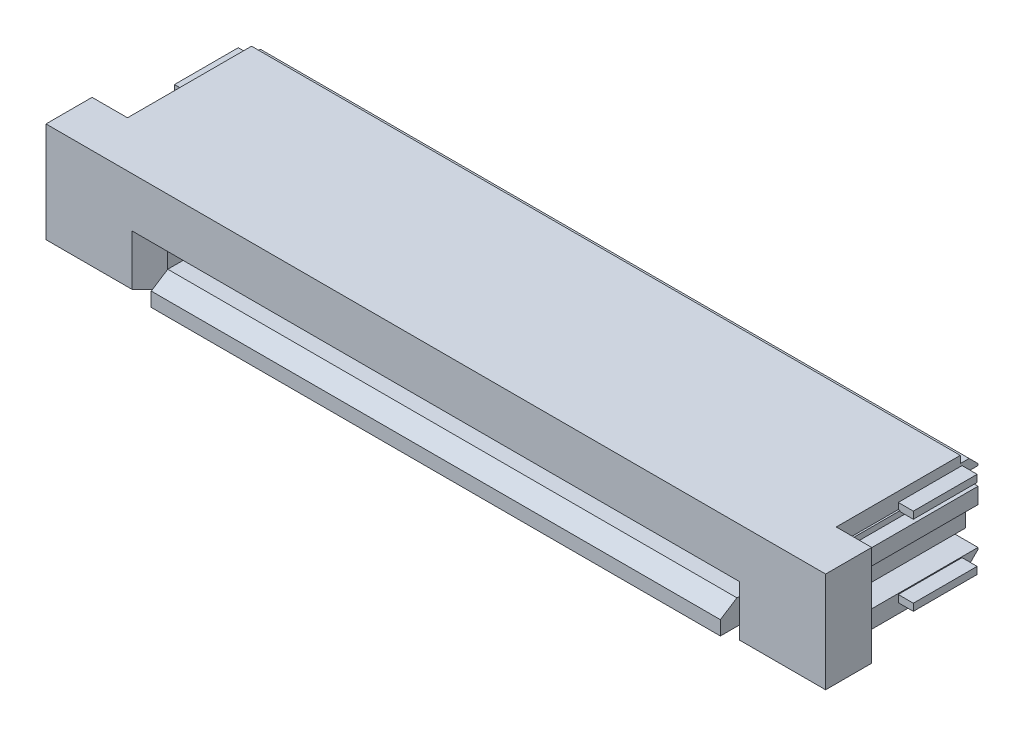
SolidWorks part; units mm, degrees
material "policarbonato"
ref_plane "Front" through (0, 0, 0) normal (0, 0, 1) x (1, 0, 0)
ref_plane "Top" through (0, 0, 0) normal (0, 1, 0) x (1, 0, 0)
ref_plane "Side" through (0, 0, 0) normal (1, 0, 0) x (0, 0, -1)
sketch "Sketch1" plane through (0, 0, 0) normal (1, 0, 0) x (0, 0, -1)
  line L0 (-1.75, 1.5) -> (1.75, 1.5)
  line L1 (2, 1.3) -> (1.75, 1.3)
  line L2 (1.75, 1.5) -> (1.75, 1.3)
  line L3 (2.25, 1.05) -> (2, 1.3)
  line L4 (2.25, -1.05) -> (2.25, 1.05)
  line L5 (2, -1.3) -> (2.25, -1.05)
  line L6 (1.75, -1.3) -> (1.75, -1.5)
  line L7 (2, -1.3) -> (1.75, -1.3)
  line L8 (-3.05, -1.5) -> (1.75, -1.5)
  line L9 (-1.75, -0.65) -> (-1.75, 1.5)
  line L10 (-2.35, -0.65) -> (-1.75, -0.65)
  line L11 (-2.35, -0.65) -> (-3.05, -1.1)
  line L12 (-3.05, -1.5) -> (-3.05, -1.1)
  line L13 (-1.75, 1.5) -> (1.75, -1.5) construction
  point P1 (0, 0)
  dimension "D1" = 45
  dimension "D2" = 45
  dimension "D3" = 3.5
  dimension "D4" = 0.25
  dimension "D5" = 0.5
  dimension "D6" = 0.2
  dimension "D7" = 1.3
  dimension "D8" = 32.735
  dimension "D9" = 0.6
  dimension "D10" = 3
  dimension "D11" = 0.4
  dimension "D12" = 0.2
extrude "Base" add sketch "Sketch1" along normal mid plane 20
sketch "Sketch2" plane through (0, 0, 3.05) normal (0, 0, 1) x (1, 0, 0)
  line L0 (10, -1.5) -> (-10, -1.5) construction
  line L1 (-8.1, 0.75) -> (8.1, 0.75)
  line L2 (-8.1, 0.75) -> (-8.1, -0.8)
  line L3 (-8.1, -0.8) -> (8.1, -0.8)
  line L4 (8.1, 0.75) -> (8.1, -0.8)
  line L5 (10, 1.5) -> (-10, 1.5) construction
  line L6 (-10, 1.5) -> (-10, -0.65) construction
  line L7 (10, 1.5) -> (10, -0.65) construction
  dimension "D1" = 0.7
  dimension "D2" = 0.75
  dimension "D3" = 1.9
  dimension "D4" = 1.9
extrude "Card Slot" cut sketch "Sketch2" against normal blind 3.8
sketch "Sketch4" plane through (0, 0, 1.75) normal (0, 0, 1) x (1, 0, 0)
  line L0 (10, 1.5) -> (10, -0.65) construction
  line L1 (-10, 1) -> (-8.225, 1)
  line L2 (-10, 1) -> (-10, -1)
  line L3 (-10, -1) -> (-8.225, -1)
  line L4 (-8.225, 1) -> (-8.225, -1)
  line L5 (10, 1) -> (8.225, 1)
  line L6 (10, 1) -> (10, -1)
  line L7 (10, -1) -> (8.225, -1)
  line L8 (8.225, 1) -> (8.225, -1)
  line L9 (10, -1.5) -> (-10, -1.5) construction
  line L11 (10, 1.5) -> (-10, 1.5) construction
  line L12 (-10, 1.5) -> (-10, -0.65) construction
  dimension "D1" = 0.5
  dimension "D2" = 0.5
  dimension "D3" = 1.775
extrude "Wings" cut sketch "Sketch4" against normal through all
sketch "Sketch5" plane through (0, 0, 3.05) normal (0, 0, 1) x (1, 0, 0)
  line L0 (10, -1.5) -> (-10, -1.5) construction
  line L1 (-10, 1.5) -> (-8.03, 1.5)
  line L2 (-10, 1.5) -> (-10, -1.5)
  line L3 (-10, -1.5) -> (-8.03, -1.5)
  line L4 (-8.03, 1.5) -> (-8.03, -1.5)
  line L5 (0, 0) -> (0, 2.0181) construction
  line L6 (10, 1.5) -> (8.03, 1.5)
  line L7 (10, 1.5) -> (10, -1.5)
  line L8 (10, -1.5) -> (8.03, -1.5)
  line L9 (8.03, 1.5) -> (8.03, -1.5)
  dimension "D1" = 1.97
extrude "Front Lead In" cut sketch "Sketch5" against normal up to surface (1.3 mm away) up to face at (0, 0.4917, 1.75)
chamfer "Card Slot Lead In" distance 0.1 angle 60 3 edges at (8.1, -0.025, 1.75) (0, 0.75, 1.75) (-8.1, -0.025, 1.75)
ref_plane "POS 1 Plane" through (7, 0, 0) normal (1, 0, 0) x (0, 0, -1)
ref_plane "WT Plane" through (0, 0, 0) normal (0, 0, 1) x (1, 0, 0)
sketch "Sketch8" plane through (0, 0, 0) normal (0, 0, 1) x (1, 0, 0)
  line L0 (0, 0) -> (0, 411) construction
  line L1 (-10, -1) -> (-10, -1.5) construction
  line L4 (10, -1.5) -> (10, -1.3) construction
  line L5 (10, 1.5) -> (-10, 1.5) construction
  point P8 (10, -1.4)
  line B0 (-10.425, 1.025) -> (-8.575, 1.025)
  line B1 (-8.575, 1.225) -> (-10.425, 1.225)
  line B2 (-10.425, 1.025) -> (-10.425, 1.225)
  line B3 (-8.225, -0.875) -> (-8.225, 0.875)
  line B4 (-8.425, 0.875) -> (-8.425, -0.875)
  line B5 (-8.575, -1.025) -> (-10.425, -1.025)
  line B6 (-10.425, -1.225) -> (-10.425, -1.025)
  line B7 (-10.425, -1.225) -> (-8.575, -1.225)
  arc B8 (-8.225, 0.875) -> (-8.575, 1.225) centre (-8.575, 0.875) ccw
  arc B9 (-8.425, 0.875) -> (-8.575, 1.025) centre (-8.575, 0.875) ccw
  arc B10 (-8.575, -1.225) -> (-8.225, -0.875) centre (-8.575, -0.875) ccw
  arc B11 (-8.575, -1.025) -> (-8.425, -0.875) centre (-8.575, -0.875) ccw
  line B12 (10.425, 1.025) -> (8.575, 1.025)
  line B13 (8.575, 1.225) -> (10.425, 1.225)
  line B14 (10.425, 1.025) -> (10.425, 1.225)
  line B15 (8.225, -0.875) -> (8.225, 0.875)
  line B16 (8.425, 0.875) -> (8.425, -0.875)
  line B17 (8.575, -1.025) -> (10.425, -1.025)
  line B18 (10.425, -1.225) -> (10.425, -1.025)
  line B19 (10.425, -1.225) -> (8.575, -1.225)
  arc B20 (8.225, 0.875) -> (8.575, 1.225) centre (8.575, 0.875) cw
  arc B21 (8.425, 0.875) -> (8.575, 1.025) centre (8.575, 0.875) cw
  arc B22 (8.575, -1.225) -> (8.225, -0.875) centre (8.575, -0.875) cw
  arc B23 (8.575, -1.025) -> (8.425, -0.875) centre (8.575, -0.875) cw
  dimension "D1" = 0.425
  dimension "D2" = 0.425
  dimension "D3" = 0.275
sketch_block_instance "Block2-1"
sketch_block "Block2"
sketch_block_instance "Block2-3"
extrude "WT" add sketch "Sketch8" against normal blind 1.8
sketch "Sketch9" plane through (0, 0, 1.75) normal (0, 0, 1) x (1, 0, 0)
  line L1 (-10, -1.5) -> (-8.03, -1.5) construction
  line L2 (8.07, 0.1) -> (8.07, -1.33)
  line L3 (-8.07, 0.1) -> (8.07, 0.1)
  line L4 (8.07, -1.33) -> (11, -1.33)
  line L5 (11, -1.33) -> (11, 1.5)
  line L6 (11, 1.5) -> (-11, 1.5)
  line L7 (-11, 1.5) -> (-11, -1.33)
  line L8 (-11, -1.33) -> (-8.07, -1.33)
  line L9 (-8.07, -1.33) -> (-8.07, 0.1)
  line L10 (-10.425, 1.225) -> (-10.425, 1.025) construction
  point P2 (0, 0.1)
  dimension "D1" = 0.1
  dimension "D2" = 2.83
  dimension "D3" = 2.93
  dimension "D4" = 0.575
  dimension "D5" = 0.17
extrude "Gate" add sketch "Sketch9" along normal blind 1.3
chamfer "Gate Chamfer" distance 0.5 angle 45 2 edges at (8.07, -0.615, 3.05) (-8.07, -0.615, 3.05)
sketch "Sketch10" plane through (0, 0, 1.75) normal (0, 0, -1) x (-1, 0, 0)
  line L0 (-11, -1.33) -> (-11, 1.5) construction
  line L1 (-10.05, -0.3) -> (-10.05, 0.4451)
  line L2 (-9.5, -0.3) -> (-10.05, -0.3)
  line L3 (-11, 1.5) -> (-10, 1.5) construction
  line L4 (9.125, -0.2019) -> (9.125, 0.3755)
  line L5 (0, 0) -> (0, 3.8889) construction
  line L6 (-9.4, 0.3755) -> (-9.125, 0.3755)
  line L7 (-9.4, 0.3755) -> (-9.4, 1.05)
  line L8 (-9.4, 1.05) -> (-10.05, 1.05)
  line L9 (-10.05, 1.05) -> (-10.05, 0.8951)
  line L10 (-10.05, 0.8951) -> (-10.4, 0.8951)
  line L11 (-10.4, 0.8951) -> (-10.4, 0.4451)
  line L12 (-10.4, 0.4451) -> (-10.05, 0.4451)
  line L13 (9.5, -0.2019) -> (9.125, -0.2019)
  line L14 (-9.5, -0.3) -> (-9.5, -0.2019)
  line L15 (-9.5, -0.2019) -> (-9.125, -0.2019)
  line L16 (9.5, -0.3) -> (9.5, -0.2019)
  line L17 (-9.125, -0.2019) -> (-9.125, 0.3755)
  line L18 (10.4, 0.4451) -> (10.05, 0.4451)
  line L19 (10.4, 0.8951) -> (10.4, 0.4451)
  line L20 (10.05, 0.8951) -> (10.4, 0.8951)
  line L21 (10.05, 1.05) -> (10.05, 0.8951)
  line L22 (9.4, 1.05) -> (10.05, 1.05)
  line L23 (9.4, 0.3755) -> (9.4, 1.05)
  line L24 (9.4, 0.3755) -> (9.125, 0.3755)
  line L25 (9.5, -0.3) -> (10.05, -0.3)
  line L26 (10.05, -0.3) -> (10.05, 0.4451)
  dimension "D1" = 1.35
  dimension "D2" = 0.65
  dimension "D3" = 0.35
  dimension "D4" = 0.45
  dimension "D5" = 0.35
  dimension "D6" = 0.7451
  dimension "D7" = 0.55
  dimension "D8" = 0.0981
  dimension "D9" = 0.375
  dimension "D10" = 0.6
  dimension "D11" = 0.45
  dimension "D12" = 0.275
  dimension "D13" = 0.6745
extrude "Gate Guide" add sketch "Sketch10" along normal blind 3.6
sketch "Sketch6" plane through (7, 0, 0) normal (1, 0, 0) x (0, 0, -1)
  line L0 (-1.75, -1.5) -> (1.75, -1.5) construction
  line L3 (0.75, 0.75) -> (0.75, -0.8) construction
  line B0 (1.8966, 1.1164) -> (1.8966, 1.1134)
  line B1 (1.1383, -0.6804) -> (-1.1565, -0.4395)
  line B2 (1.1383, -0.6804) -> (1.5518, -0.6804)
  line B3 (1.8966, -0.6772) -> (1.8966, -0.6743)
  line B4 (2.2503, -0.3242) -> (2.2503, -0.6772)
  line B5 (2.2503, 0.5618) -> (2.2503, -0.1226)
  line B6 (3.7503, 1.3984) -> (3.7503, 1.3222)
  line B7 (2.5059, 0.815) -> (2.3646, 0.815)
  line B8 (3.069, 1.176) -> (2.7405, 0.9004)
  line B9 (3.6487, 1.2206) -> (3.1915, 1.2206)
  line B10 (3.1915, 1.5) -> (3.6487, 1.5)
  line B11 (2.6097, 1.1553) -> (2.8894, 1.3901)
  line B12 (1.5518, 1.1196) -> (-1.3757, 1.1196)
  line B13 (-1.0668, 0.7796) -> (-1.4132, 0.9796)
  line B14 (1.3415, 0.5196) -> (1.3415, 0.449)
  line B15 (1.0915, 0.7696) -> (-1.0293, 0.7696)
  line B16 (-1.1045, -0.2363) -> (0.5626, -0.3004)
  line B17 (-1.6498, -0.425) -> (-1.3625, -0.0694)
  arc B18 (1.6915, -0.5407) -> (1.5518, -0.6804) centre (1.5518, -0.5407) cw
  arc B19 (1.6915, -0.5407) -> (1.8966, -0.6743) centre (1.7506, -0.6743) cw
  arc B20 (2.2503, -0.6772) -> (1.8966, -0.6772) centre (2.0735, -0.6772) cw
  arc B21 (2.2503, -0.3242) -> (2.2503, -0.1226) centre (2.3646, -0.2234) cw
  arc B22 (3.6487, 1.5) -> (3.7503, 1.3984) centre (3.6487, 1.3984) cw
  arc B23 (3.7503, 1.3222) -> (3.6487, 1.2206) centre (3.6487, 1.3222) cw
  arc B24 (2.2503, 0.5618) -> (2.3646, 0.815) centre (2.3646, 0.6626) cw
  arc B25 (2.7405, 0.9004) -> (2.5059, 0.815) centre (2.5059, 1.18) cw
  arc B26 (3.069, 1.176) -> (3.1915, 1.2206) centre (3.1915, 1.0301) cw
  arc B27 (2.8894, 1.3901) -> (3.1915, 1.5) centre (3.1915, 1.0301) cw
  arc B28 (2.6097, 1.1553) -> (2.2216, 1.213) centre (2.4412, 1.3561) cw
  arc B29 (1.8966, 1.1164) -> (2.2216, 1.213) centre (2.0735, 1.1164) cw
  arc B30 (1.8966, 1.1134) -> (1.6915, 0.9799) centre (1.7506, 1.1134) cw
  arc B31 (1.5518, 1.1196) -> (1.6915, 0.9799) centre (1.5518, 0.9799) cw
  arc B32 (-1.4132, 0.9796) -> (-1.3757, 1.1196) centre (-1.3757, 1.0446) cw
  arc B33 (-1.0293, 0.7696) -> (-1.0668, 0.7796) centre (-1.0293, 0.8446) cw
  arc B34 (1.0915, 0.7696) -> (1.3415, 0.5196) centre (1.0915, 0.5196) cw
  arc B35 (1.3415, 0.449) -> (0.5626, -0.3004) centre (0.5915, 0.449) cw
  arc B36 (-1.1045, -0.2363) -> (-1.25, -0.1019) centre (-1.0986, -0.084) cw
  arc B37 (-1.3625, -0.0694) -> (-1.25, -0.1019) centre (-1.3131, -0.1093) cw
  arc B38 (-1.5704, -0.5208) -> (-1.6498, -0.425) centre (-1.6004, -0.4649) cw
  arc B39 (-1.5704, -0.5208) -> (-1.1565, -0.4395) centre (-1.2313, -1.1525) cw
  dimension "D1" = 3
  dimension "D2" = 2
sketch_block_instance "Block4-1"
sketch_block "Block4"
sketch "Sketch13" plane through (7, 0, 0) normal (1, 0, 0) x (0, 0, -1)
  line L0 (1.75, 1.5) -> (-1.75, 1.5) construction
  line L1 (0.75, -0.8) -> (0.75, 0.75) construction
  arc B0 (1.0915, -0.7696) -> (1.3415, -0.5196) centre (1.0915, -0.5196) ccw
  line B1 (1.0915, -0.7696) -> (-1.0293, -0.7696)
  line B2 (1.5518, -1.1196) -> (-1.3757, -1.1196)
  line B3 (2.2503, 0.6075) -> (-5.2255, 0.6075) construction
  line B4 (-1.6498, 0.425) -> (-1.3625, 0.0694)
  line B5 (-1.1045, 0.2363) -> (0.5626, 0.3004)
  line B6 (1.3415, -0.5196) -> (1.3415, -0.449)
  line B7 (-1.0668, -0.7796) -> (-1.4132, -0.9796)
  line B8 (2.6097, -1.1553) -> (2.8894, -1.3901)
  line B9 (3.1915, -1.5) -> (3.6487, -1.5)
  line B10 (3.6487, -1.2206) -> (3.1915, -1.2206)
  line B11 (3.069, -1.176) -> (2.7405, -0.9004)
  line B12 (2.5059, -0.815) -> (2.3646, -0.815)
  line B13 (3.7503, -1.3984) -> (3.7503, -1.3222)
  line B14 (2.2503, -0.5618) -> (2.2503, 0.1226)
  line B15 (2.2503, 0.3242) -> (2.2503, 0.6772)
  line B16 (1.8966, 0.6772) -> (1.8966, 0.6742)
  line B17 (1.1383, 0.6804) -> (1.5518, 0.6804)
  line B18 (1.1383, 0.6804) -> (-1.1565, 0.4395)
  line B19 (1.8966, -1.1135) -> (1.8966, -1.1164)
  arc B20 (-1.5704, 0.5208) -> (-1.1565, 0.4395) centre (-1.2313, 1.1525) ccw
  arc B21 (-1.5704, 0.5208) -> (-1.6498, 0.425) centre (-1.6004, 0.4649) ccw
  arc B22 (-1.3625, 0.0694) -> (-1.25, 0.1019) centre (-1.3131, 0.1093) ccw
  arc B23 (-1.1045, 0.2363) -> (-1.25, 0.1019) centre (-1.0986, 0.084) ccw
  arc B24 (1.3415, -0.449) -> (0.5626, 0.3004) centre (0.5915, -0.449) ccw
  arc B25 (-1.0293, -0.7696) -> (-1.0668, -0.7796) centre (-1.0293, -0.8446) ccw
  arc B26 (-1.4132, -0.9796) -> (-1.3757, -1.1196) centre (-1.3757, -1.0446) ccw
  arc B27 (1.5518, -1.1196) -> (1.6915, -0.9799) centre (1.5518, -0.9799) ccw
  arc B28 (1.8966, -1.1135) -> (1.6915, -0.9799) centre (1.7506, -1.1135) ccw
  arc B29 (1.8966, -1.1164) -> (2.2216, -1.213) centre (2.0735, -1.1164) ccw
  arc B30 (2.6097, -1.1553) -> (2.2216, -1.213) centre (2.4412, -1.3561) ccw
  arc B31 (2.8894, -1.3901) -> (3.1915, -1.5) centre (3.1915, -1.0301) ccw
  arc B32 (3.069, -1.176) -> (3.1915, -1.2206) centre (3.1915, -1.0301) ccw
  arc B33 (2.7405, -0.9004) -> (2.5059, -0.815) centre (2.5059, -1.18) ccw
  arc B34 (2.2503, -0.5618) -> (2.3646, -0.815) centre (2.3646, -0.6626) ccw
  arc B35 (3.7503, -1.3222) -> (3.6487, -1.2206) centre (3.6487, -1.3222) ccw
  arc B36 (3.6487, -1.5) -> (3.7503, -1.3984) centre (3.6487, -1.3984) ccw
  arc B37 (2.2503, 0.3242) -> (2.2503, 0.1226) centre (2.3646, 0.2234) ccw
  arc B38 (2.2503, 0.6772) -> (1.8966, 0.6772) centre (2.0735, 0.6772) ccw
  arc B39 (1.6915, 0.5407) -> (1.8966, 0.6742) centre (1.7506, 0.6742) ccw
  arc B40 (1.6915, 0.5407) -> (1.5518, 0.6804) centre (1.5518, 0.5407) ccw
  dimension "D1" = 3
  dimension "D2" = 2
sketch_block_instance "Block1-5"
sketch_block "Block1" parameters "D1"=5.4663
extrude "-01 Contact" add sketch "Sketch13" along normal mid plane 0.25
pattern_linear "LPattern3" count 15 spacing 1 along (-1, 0, 0) of "-01 Contact"
